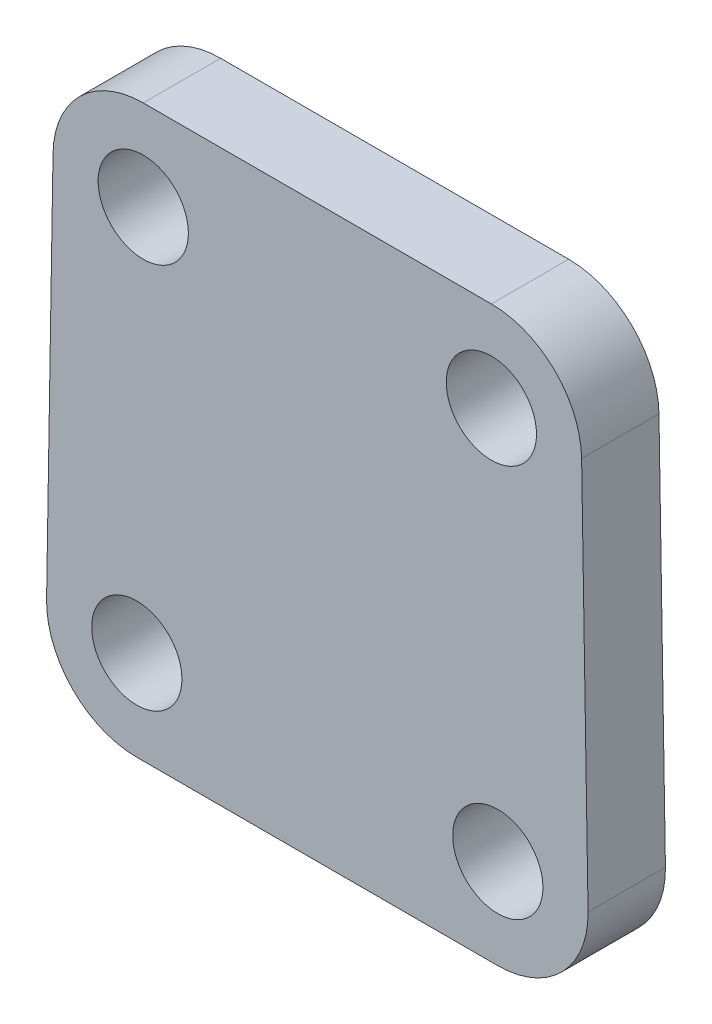
SolidWorks part; units mm, degrees
ref_plane "Plan de face" through (0, 0, 0) normal (0, 0, 1) x (1, 0, 0)
ref_plane "Plan de dessus" through (0, 0, 0) normal (0, 1, 0) x (1, 0, 0)
ref_plane "Plan de droite" through (0, 0, 0) normal (1, 0, 0) x (0, 0, -1)
sketch "Esquisse1" plane through (0, 0, 0) normal (0, 0, 1) x (1, 0, 0)
  line L0 (-7, -3.8) -> (7, -3.8) construction
  line L9 (-6.75, 11.3) -> (6.75, 11.3) construction
  line L10 (0, 0) -> (0, -3.8) construction
  line L11 (0, 0) -> (0, 11.3) construction
  line L12 (-10.5579, -7.3) -> (-10.1921, 14.8)
  line L17 (-10.1921, 14.8) -> (10.1921, 14.8)
  line L18 (10.1921, 14.8) -> (10.5579, -7.3)
  line L19 (10.5579, -7.3) -> (-10.5579, -7.3)
  line L20 (6.75, 9.55) -> (6.75, 13.05) construction
  line L21 (6.75, 11.3) -> (10.25, 11.3) construction
  line L22 (6.75, 11.3) -> (6.75, 14.8) construction
  line L23 (-7, -3.8) -> (-7, -7.3) construction
  line L24 (-7, -3.8) -> (-10.5, -3.8) construction
  circle A2 centre (-6.75, 11.3) radius 1.75
  circle A3 centre (6.75, 11.3) radius 1.75
  circle A4 centre (-7, -3.8) radius 1.75
  circle A5 centre (7, -3.8) radius 1.75
  point P8 (0, 11.3)
  point P21 (0, 14.8)
  point P24 (0, -7.3)
  dimension "D2" = 14
  dimension "D3" = 3.5
  dimension "D1" = 13.5
  dimension "D4" = 3.8
  dimension "D5" = 11.3
extrude "Boss.-Extru.1" add sketch "Esquisse1" along normal blind 3
fillet "Congé1" radius 3.5 4 edges at (-10.1921, 14.8, 1.5) (10.1921, 14.8, 1.5) (10.5579, -7.3, 1.5) (-10.5579, -7.3, 1.5)
